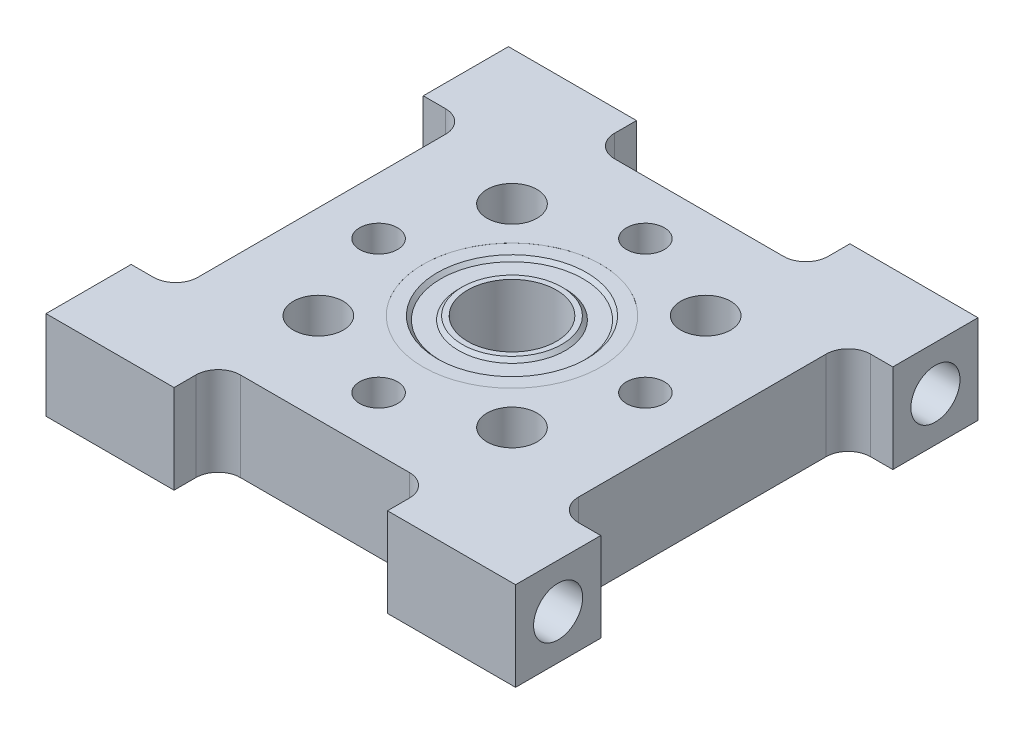
SolidWorks part; units mm, degrees
material "6061 Alloy"
ref_plane "Front Plane" through (0, 0, 0) normal (0, 0, 1) x (1, 0, 0)
ref_plane "Top Plane" through (0, 0, 0) normal (0, 1, 0) x (1, 0, 0)
ref_plane "Right Plane" through (0, 0, 0) normal (1, 0, 0) x (0, 0, -1)
sketch "Sketch1" plane through (0, 0, 0) normal (0, 1, 0) x (1, 0, 0)
  line L0 (-16.764, 0) -> (16.764, 0) construction
  line L1 (-16.764, -16.51) -> (-7.62, -16.51)
  line L2 (-16.764, -16.51) -> (-16.764, -10.4267)
  line L3 (-16.764, 16.51) -> (-7.62, 16.51)
  line L4 (16.764, -16.51) -> (16.764, -10.4267)
  line L5 (-16.764, -16.51) -> (16.764, 16.51) construction
  line L6 (-16.764, 16.51) -> (16.764, -16.51) construction
  line L7 (0, 16.51) -> (0, -16.51) construction
  line L8 (-7.62, -16.51) -> (-7.62, -14.9479)
  line L9 (-6.0325, -13.3604) -> (6.0325, -13.3604)
  line L10 (7.62, -14.9479) -> (7.62, -16.51)
  line L11 (7.62, -16.51) -> (16.764, -16.51)
  line L12 (7.62, 14.9479) -> (7.62, 16.51)
  line L13 (-6.0325, 13.3604) -> (6.0325, 13.3604)
  line L14 (-7.62, 16.51) -> (-7.62, 14.9479)
  line L15 (7.62, 16.51) -> (16.764, 16.51)
  line L16 (-16.764, 10.4267) -> (-15.1765, 10.4267)
  line L17 (-13.589, 8.8392) -> (-13.589, -8.8392)
  line L18 (-15.1765, -10.4267) -> (-16.764, -10.4267)
  line L19 (-16.764, 10.4267) -> (-16.764, 16.51)
  line L20 (15.1765, -10.4267) -> (16.764, -10.4267)
  line L21 (13.589, 8.8392) -> (13.589, -8.8392)
  line L22 (16.764, 10.4267) -> (15.1765, 10.4267)
  line L23 (16.764, 10.4267) -> (16.764, 16.51)
  arc A0 (6.0325, -13.3604) -> (7.62, -14.9479) centre (6.0325, -14.9479) cw
  arc A1 (-7.62, -14.9479) -> (-6.0325, -13.3604) centre (-6.0325, -14.9479) cw
  arc A2 (-7.62, 14.9479) -> (-6.0325, 13.3604) centre (-6.0325, 14.9479) ccw
  arc A3 (6.0325, 13.3604) -> (7.62, 14.9479) centre (6.0325, 14.9479) ccw
  arc A4 (-13.589, -8.8392) -> (-15.1765, -10.4267) centre (-15.1765, -8.8392) cw
  arc A5 (-15.1765, 10.4267) -> (-13.589, 8.8392) centre (-15.1765, 8.8392) cw
  arc A6 (15.1765, 10.4267) -> (13.589, 8.8392) centre (15.1765, 8.8392) ccw
  arc A7 (13.589, -8.8392) -> (15.1765, -10.4267) centre (15.1765, -8.8392) ccw
  circle A8 centre (0, 0) radius 5.3975
  point P0 (0, 0)
  dimension "D6" = 1.5875
  dimension "D10" = 1.5875
  dimension "D11" = 10.795
  dimension "D1" = 33.02
  dimension "D2" = 33.528
  dimension "D3" = 15.24
  dimension "D4" = 7.62
  dimension "D5" = 3.1496
  dimension "D7" = 20.8534
  dimension "D8" = 10.4267
  dimension "D9" = 3.175
extrude "Boss-Extrude1" add sketch "Sketch1" along normal blind 6.35
sketch "Sketch2" plane through (0, 6.35, 0) normal (0, 1, 0) x (1, 0, 0)
  circle A0 centre (0, 0) radius 6.35
  dimension "D1" = 12.7
extrude "Cut-Extrude1" cut sketch "Sketch2" against normal blind 4.7625
ref_plane "Plane1" through (0, 1.5875, 0) normal (0, 1, 0) x (-1, 0, 0)
sketch "Sketch3" plane through (0, 1.5875, 0) normal (0, 1, 0) x (-1, 0, 0)
  circle A0 centre (0, 0) radius 6.35
  circle A1 centre (0, 0) radius 5.08
  dimension "D2" = 10.16
  dimension "D1" = 1.27
extrude "Boss-Extrude2" add sketch "Sketch3" along normal blind 4.76
chamfer "Chamfer1" distance 0.254 angle 45 2 edges at (0, 1.5875, 5.08) (0, 6.3475, 5.08)
sketch "Sketch4" plane through (0, 1.5875, 0) normal (0, 1, 0) x (-1, 0, 0)
  circle A0 centre (0, 0) radius 3.175
  circle A1 centre (0, 0) radius 3.81
  dimension "D1" = 6.35
  dimension "D2" = 0.635
extrude "Boss-Extrude3" add sketch "Sketch4" along normal blind 4.76 separate body
chamfer "Chamfer2" distance 0.254 angle 45 2 edges at (0, 1.5875, 3.81) (0, 6.3475, 3.81)
ref_plane "Plane2" through (0, 6.0935, 0) normal (0, 1, 0) x (-1, 0, 0)
sketch "Sketch5" plane through (0, 6.0935, 0) normal (0, 1, 0) x (-1, 0, 0)
  circle A0 centre (0, 0) radius 5.08
  circle A1 centre (0, 0) radius 3.81
  dimension "D1" = 10.16
  dimension "D2" = 7.62
extrude "Boss-Extrude4" add sketch "Sketch5" against normal blind 4.2545
hole_wizard "#6-32 Tapped Hole1" positions "Sketch9" profile "Sketch8" tap size "#6-32" standard "Ansi Inch"
sketch "Sketch9" plane through (-16.764, 0, 0) normal (-1, 0, 0) x (0, 0, 1)
  line L0 (-13.4704, 3.175) -> (13.4704, 3.175) construction
  line L1 (-13.4704, 3.175) -> (0, 16.6454) construction
  line L2 (13.4704, 3.175) -> (0, 16.6454) construction
  line L3 (-16.51, 0) -> (-10.4267, 0) construction
  point P0 (-13.4704, 3.175)
  point P1 (13.4704, 3.175)
  dimension "D1" = 19.05
  dimension "D2" = 19.05
  dimension "D3" = 3.175
sketch "Sketch8" plane through (-16.764, 3.175, -13.4704) normal (0, 1, 0) x (0, 0, 1)
  line L0 (0, 0) -> (0, 8.7629)
  line L1 (0, 8.7629) -> (1.3525, 7.9502)
  line L2 (1.3525, 7.9502) -> (1.3525, 7.0104)
  line L3 (1.3525, 7.0104) -> (1.7526, 7.0104)
  line L4 (1.7526, 7.0104) -> (1.7526, 0)
  line L5 (1.7526, 0) -> (0, 0)
  line L10 (0, 8.7629) -> (-1.3526, 7.9502) construction
  line L11 (0, -6.35) -> (0, 107.95) construction
  dimension "Tap Drill Dia." = 2.7051
  dimension "Tap Drill Depth" = 7.9502
  dimension "Thread Major Dia." = 3.5052
  dimension "Thread Depth" = 7.0104
  dimension "Drill Angle" = 118
mirror "Mirror1" about plane through (0, 0, 0) normal (1, 0, 0) of "#6-32 Tapped Hole1"
hole_wizard "#6-32 Tapped Hole2" positions "Sketch11" profile "Sketch10" tap size "#6-32" standard "Ansi Inch" end condition up to next
sketch "Sketch11" plane through (0, 6.35, 0) normal (0, 1, 0) x (-1, 0, 0)
  point P0 (0, -9.525)
  point P8 (-9.525, 0)
  point P9 (0, 9.525)
  point P10 (9.525, 0)
  dimension "D1" = 9.525
  dimension "D2" = 4
sketch "Sketch10" plane through (0, 6.35, -9.525) normal (1, 0, 0) x (0, 0, 1)
  line L0 (0, 0) -> (0, 6.35)
  line L1 (0, 6.35) -> (1.3525, 6.35)
  line L2 (1.3525, 6.35) -> (1.3525, 0)
  line L5 (1.3525, 0) -> (0, 0)
  line L11 (0, -6.35) -> (0, 107.95) construction
  dimension "Thru Tap Drill Dia." = 2.7051
  dimension "Thru Tap Drill Depth" = 6.35
cosmetic thread "Hole Thread1" parameters "D2"=3.5052
cosmetic thread "Hole Thread2" parameters "D2"=3.5052
cosmetic thread "Hole Thread3" parameters "D2"=3.5052
cosmetic thread "Hole Thread4" parameters "D2"=3.5052
hole_wizard "9/64 (0.14063) Diameter Hole1" positions "Sketch13" profile "Sketch12" hole size "9/64" standard "Ansi Inch"
sketch "Sketch13" plane through (0, 6.35, 0) normal (0, 1, 0) x (-1, 0, 0)
  line L0 (0, 0) -> (6.9148, -6.9148) construction
  line L2 (0, 0) -> (13.589, 0) construction
  line L3 (13.589, -8.8392) -> (13.589, 8.8392) construction
  point P0 (6.9148, -6.9148)
  point P21 (-6.9148, -6.9148)
  point P22 (-6.9148, 6.9148)
  point P23 (6.9148, 6.9148)
  dimension "D1" = 9.779
  dimension "D2" = 45
  dimension "D3" = 4
sketch "Sketch12" plane through (-6.9148, 6.35, -6.9148) normal (1, 0, 0) x (0, 0, 1)
  line L0 (0, 0) -> (0, 7.4231)
  line L1 (0, 7.4231) -> (1.786, 6.35)
  line L2 (1.786, 6.35) -> (1.786, 0)
  line L5 (1.786, 0) -> (0, 0)
  line L10 (0, 7.4231) -> (-1.786, 6.35) construction
  line L11 (0, -6.35) -> (0, 107.95) construction
  dimension "Hole Dia." = 3.572
  dimension "Hole Depth" = 6.35
  dimension "Drill Angle" = 118
